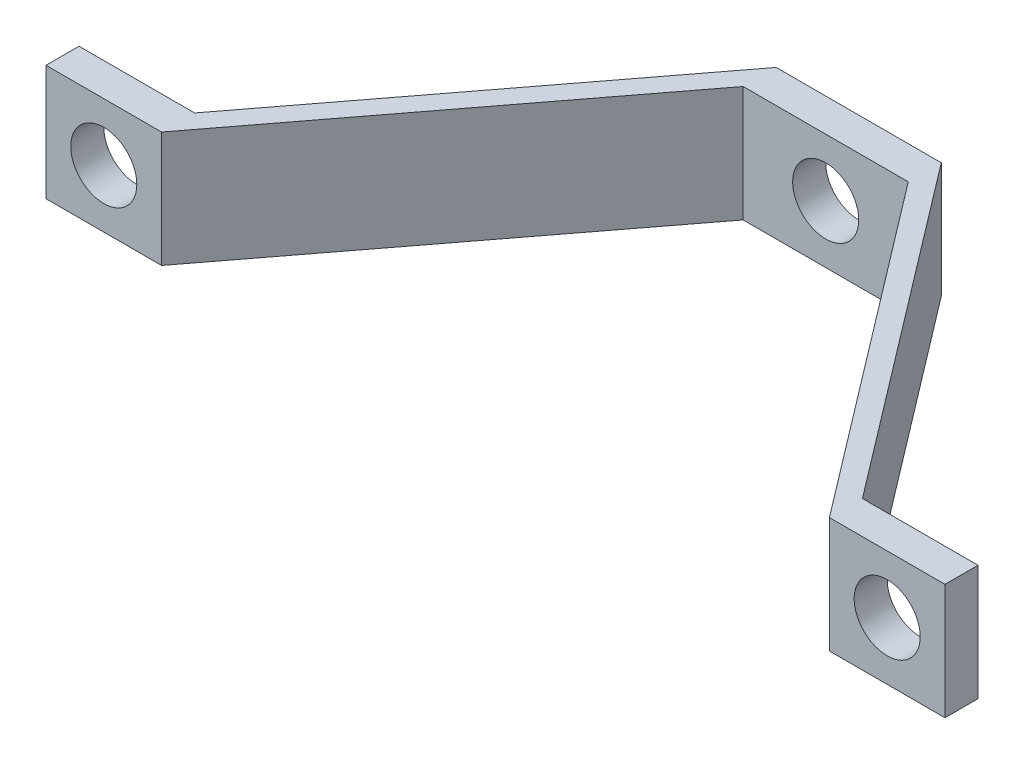
SolidWorks part; units mm, degrees
ref_plane "Front Plane" through (0, 0, 0) normal (0, 0, 1) x (1, 0, 0)
ref_plane "Top Plane" through (0, 0, 0) normal (0, 1, 0) x (1, 0, 0)
ref_plane "Right Plane" through (0, 0, 0) normal (1, 0, 0) x (0, 0, -1)
sketch "Sketch1" plane through (0, 0, 0) normal (0, 1, 0) x (1, 0, 0)
  line L0 (6.35, 0) -> (-6.35, 0)
  line L1 (-6.35, 0) -> (-25.6845, -25.4)
  line L2 (-25.6845, -25.4) -> (-34.5745, -25.4)
  line L3 (-34.5745, -25.4) -> (-34.5745, -27.94)
  line L4 (-34.5745, -27.94) -> (-25.6845, -27.94)
  line L5 (-25.6845, -27.94) -> (-6.35, -2.54)
  line L6 (-6.35, -2.54) -> (6.35, -2.54)
  line L7 (0, 0) -> (0, -6.3382) construction
  line L8 (0, 0) -> (0, -2.54) construction
  line L9 (-6.35, 0) -> (-6.35, -27.94) construction
  line L10 (-6.35, -27.94) -> (-25.6845, -27.94) construction
  line L11 (25.6845, -27.94) -> (6.35, -2.54)
  line L12 (34.5745, -27.94) -> (25.6845, -27.94)
  line L13 (34.5745, -25.4) -> (34.5745, -27.94)
  line L14 (25.6845, -25.4) -> (34.5745, -25.4)
  line L15 (6.35, 0) -> (25.6845, -25.4)
  line L16 (-30.1295, -25.4) -> (-30.1295, -27.94) construction
  line L17 (30.1295, -25.4) -> (30.1295, -27.94) construction
  line L18 (30.1295, -26.67) -> (-30.1295, -26.67) construction
  point P15 (0, -2.54)
  point P16 (0, 0)
  dimension "D1" = 6.35
  dimension "D2" = 8.89
  dimension "D3" = 2.54
  dimension "D4" = 2.54
  dimension "D5" = 27.94
  dimension "D7" = 60.259
extrude "Boss-Extrude1" add sketch "Sketch1" along normal blind 8.89
sketch "Sketch2" plane through (0, 0, 27.94) normal (0, 0, 1) x (1, 0, 0)
  line L0 (-30.1295, 8.89) -> (-30.1295, 0) construction
  line L1 (-34.5745, 8.89) -> (-25.6845, 8.89) construction
  line L2 (-34.5745, 0) -> (-25.6845, 0) construction
  line L3 (-34.5745, 4.445) -> (-25.6845, 4.445) construction
  line L4 (-34.5745, 8.89) -> (-34.5745, 0) construction
  line L5 (-25.6845, 8.89) -> (-25.6845, 0) construction
  circle A0 centre (-30.1295, 4.445) radius 2.54
  dimension "D1" = 5.08
extrude "Cut-Extrude1" cut sketch "Sketch2" against normal through all
sketch "Sketch3" plane through (0, 0, 27.94) normal (0, 0, 1) x (1, 0, 0)
  line L0 (30.1295, 8.89) -> (30.1295, 0) construction
  line L1 (25.6845, 8.89) -> (34.5745, 8.89) construction
  line L2 (25.6845, 0) -> (34.5745, 0) construction
  circle A0 centre (30.1295, 4.445) radius 2.54
  dimension "D1" = 5.08
extrude "Cut-Extrude2" cut sketch "Sketch3" against normal through all
sketch "Sketch4" plane through (0, 0, 2.54) normal (0, 0, 1) x (1, 0, 0)
  line L0 (0, 8.89) -> (0, 0) construction
  line L1 (-6.35, 8.89) -> (6.35, 8.89) construction
  circle A0 centre (0, 4.445) radius 2.54
  dimension "D1" = 5.08
extrude "Cut-Extrude3" cut sketch "Sketch4" against normal blind 8.89
